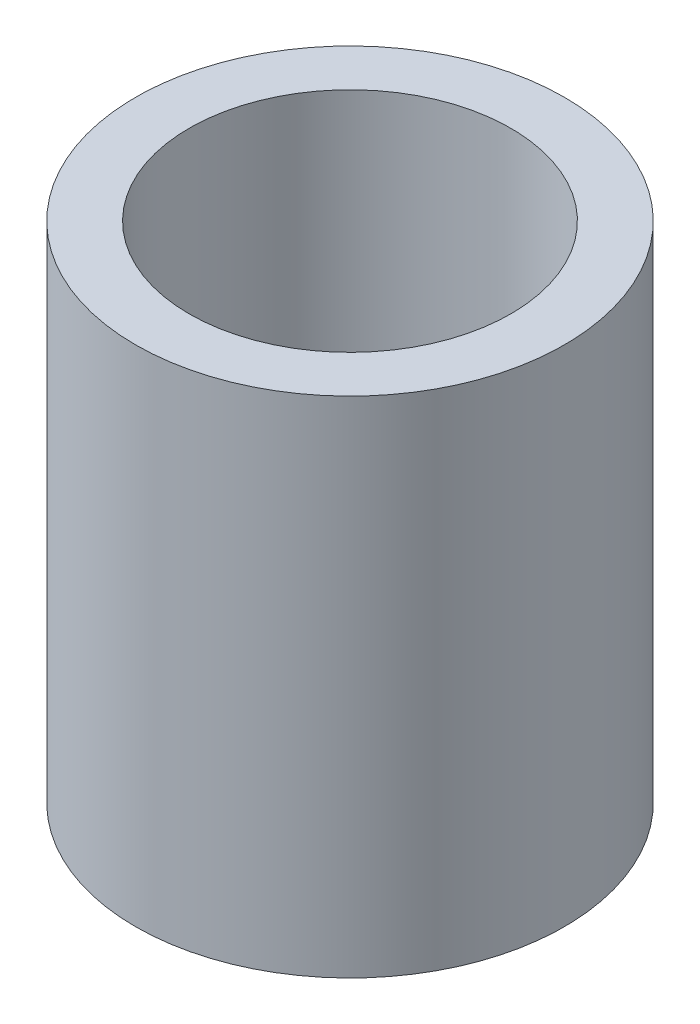
SolidWorks part; units mm, degrees
material "Brass"
ref_plane "Front Plane" through (0, 0, 0) normal (0, 0, 1) x (1, 0, 0)
ref_plane "Top Plane" through (0, 0, 0) normal (0, 1, 0) x (1, 0, 0)
ref_plane "Right Plane" through (0, 0, 0) normal (1, 0, 0) x (0, 0, -1)
sketch "Sketch1" plane through (0, 0, 0) normal (0, 1, 0) x (1, 0, 0)
  circle A0 centre (0, 0) radius 2
  circle A1 centre (0, 0) radius 1.5
  dimension "D1" = 3
  dimension "D2" = 4
extrude "Boss-Extrude1" add sketch "Sketch1" along normal blind 4.7
